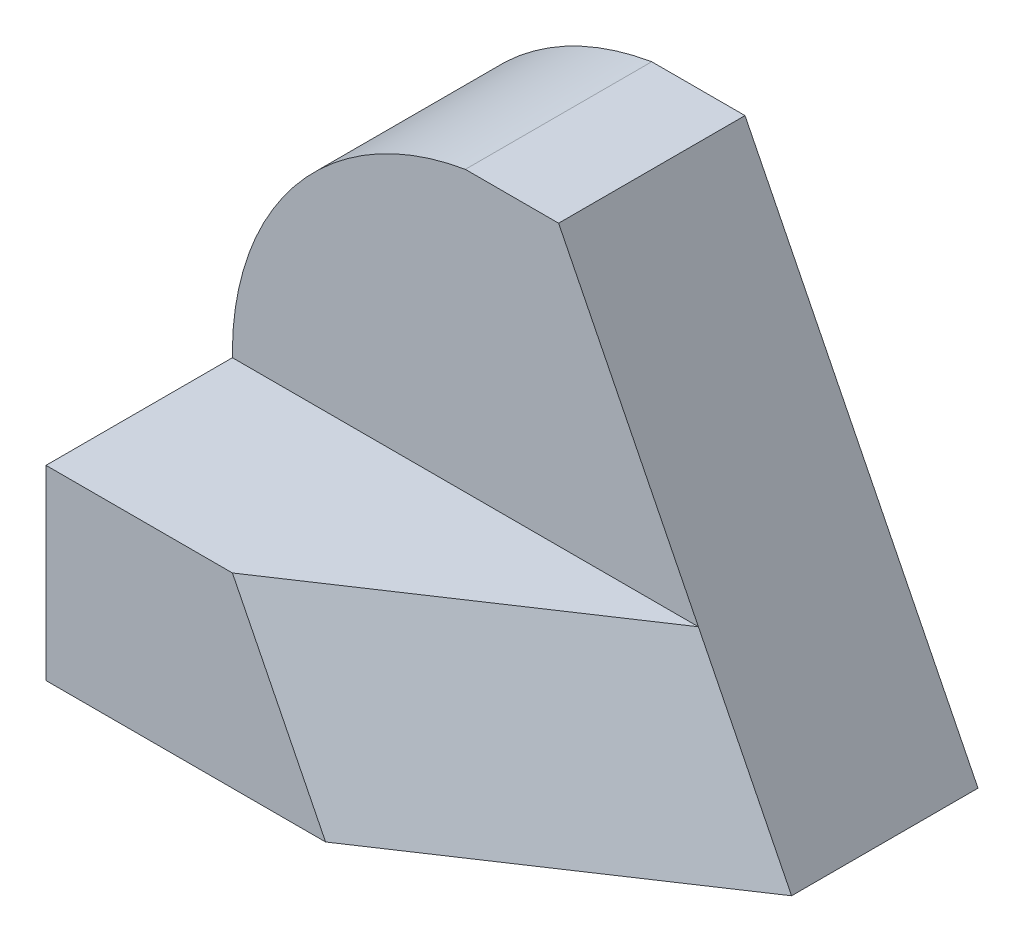
SolidWorks part; units mm, degrees
ref_plane "Front Plane" through (0, 0, 0) normal (0, 0, 1) x (1, 0, 0)
ref_plane "Top Plane" through (0, 0, 0) normal (0, 1, 0) x (1, 0, 0)
ref_plane "Right Plane" through (0, 0, 0) normal (1, 0, 0) x (0, 0, -1)
sketch "Sketch1" plane through (0, 0, 0) normal (0, 0, 1) x (1, 0, 0)
  line L1 (0, 0) -> (6, 0)
  line L2 (0, 0) -> (0, 5)
  line L3 (0, 5) -> (6, 5)
  line L4 (6, 0) -> (6, 5)
  dimension "D1" = 6
  dimension "D2" = 5
extrude "Boss-Extrude1" add sketch "Sketch1" along normal blind 2
sketch "Sketch2" plane through (0, 0, 2) normal (0, 0, 1) x (1, 0, 0)
  line L0 (0, 0) -> (0, 2)
  line L1 (0, 5) -> (0, 0) construction
  line L2 (0, 2) -> (6, 2)
  line L3 (6, 2) -> (6, 0)
  line L4 (0, 0) -> (6, 0) construction
  line L5 (6, 0) -> (0, 0)
  dimension "D1" = 6
  dimension "D2" = 6
  dimension "D3" = 2
extrude "Boss-Extrude2" add sketch "Sketch2" along normal blind 2
sketch3d "3DSketch1"
  line L0 (6, 2, 4) -> (0, 2, 4) construction
  line L1 (0, 0, 4) -> (6, 0, 4) construction
  line L2 (0, 2, 4) -> (0, 0, 4) construction
  line L3 (6, 0, 4) -> (6, 0, 0) construction
  line L4 (6, 0, 2) -> (3, 0, 4)
  line L5 (3, 0, 4) -> (2, 2, 4)
  line L6 (2, 2, 4) -> (5, 2, 2)
  line L7 (5, 2, 2) -> (6, 0, 2)
  line L8 (6, 2, 2) -> (0, 2, 2) construction
  point P0 (4.9185, 2, 2)
  point P1 (2, 2, 4)
  point P3 (3, 0, 4)
  point P6 (6, 0, 2)
  dimension "D1" = 2
  dimension "D2" = 3
  dimension "D3" = 2
  dimension "D4" = 0
  dimension "D5" = 1
extrude "Cut-Extrude1" cut sketch "3DSketch1" along direction (-1, 0, 0) on the side against the normal blind 10
sketch "Sketch3" plane through (0, 0, 2) normal (0, 0, 1) x (1, 0, 0)
  line L0 (6, 0) -> (5, 2)
  line L1 (5, 2) -> (3.5, 5)
  line L2 (6, 5) -> (0, 5) construction
  line L3 (3.5, 5) -> (6, 5)
  line L4 (6, 5) -> (6, 0)
extrude "Cut-Extrude2" cut sketch "Sketch3" against normal blind 10
sketch "Sketch4" plane through (0, 0, 2) normal (0, 0, 1) x (1, 0, 0)
  line L0 (3.5, 5) -> (0, 5)
  line L1 (0, 5) -> (0, 2)
  arc A0 (0, 2) -> (3.5, 5) centre (2.9997, 2.042) cw
  line M4 (0, 5) -> (0, 2)
  dimension "D1" = 3
extrude "Cut-Extrude3" cut sketch "Sketch4" against normal blind 10 contours A0 L0 M4
